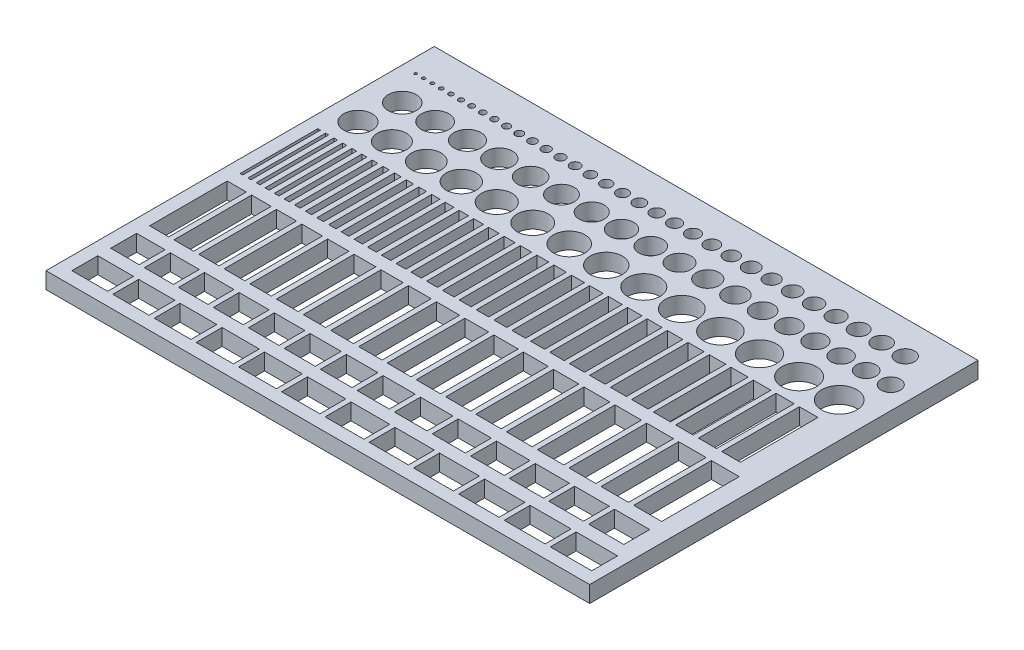
SolidWorks part; units mm, degrees
ref_plane "Front Plane" through (0, 0, 0) normal (0, 0, 1) x (1, 0, 0)
ref_plane "Top Plane" through (0, 0, 0) normal (0, 1, 0) x (1, 0, 0)
ref_plane "Right Plane" through (0, 0, 0) normal (1, 0, 0) x (0, 0, -1)
sketch "Sketch1" plane through (0, 0, 0) normal (0, 1, 0) x (1, 0, 0)
  line L1 (-105, 75) -> (105, 75)
  line L2 (-105, 75) -> (-105, -75)
  line L3 (-105, -75) -> (105, -75)
  line L4 (105, 75) -> (105, -75)
  line L5 (-105, 75) -> (105, -75) construction
  line L6 (-105, -75) -> (105, 75) construction
  point P0 (0, 0)
  dimension "D1" = 150
  dimension "D2" = 210
extrude "Boss-Extrude1" add sketch "Sketch1" along normal mid plane 6.35
sketch "Sketch2" plane through (0, 3.175, 0) normal (0, 1, 0) x (1, 0, 0)
  line L1 (-105, 75) -> (-105, -75) construction
  line L3 (105, -75) -> (105, 75) construction
  line L4 (105, 75) -> (-105, 75) construction
  circle A0 centre (-99.5, 62.3) radius 0.5
  circle A1 centre (-93.1, 62.3) radius 0.7
  circle A2 centre (-96.4, 62.3) radius 0.6
  circle A3 centre (-89.6, 62.3) radius 0.8
  circle A4 centre (-85.9, 62.3) radius 0.9
  circle A5 centre (-77.9, 62.3) radius 1.1
  circle A6 centre (-73.6, 62.3) radius 1.2
  circle A7 centre (-69.1, 62.3) radius 1.3
  circle A8 centre (-64.4, 62.3) radius 1.4
  circle A9 centre (-59.5, 62.3) radius 1.5
  circle A10 centre (-54.4, 62.3) radius 1.6
  circle A11 centre (-49.1, 62.3) radius 1.7
  circle A12 centre (-43.6, 62.3) radius 1.8
  circle A13 centre (-37.9, 62.3) radius 1.9
  circle A14 centre (-32, 62.3) radius 2
  circle A15 centre (-25.9, 62.3) radius 2.1
  circle A16 centre (-19.6, 62.3) radius 2.2
  circle A17 centre (-13.1, 62.3) radius 2.3
  circle A18 centre (-82, 62.3) radius 1
  circle A19 centre (-6.4, 62.3) radius 2.4
  circle A20 centre (0.5, 62.3) radius 2.5
  circle A21 centre (7.6, 62.3) radius 2.6
  circle A22 centre (22.4, 62.3) radius 2.8
  circle A23 centre (38, 62.3) radius 2.9
  circle A24 centre (30.1, 62.3) radius 3
  circle A25 centre (46.1, 62.3) radius 3.1
  circle A26 centre (54.4, 62.3) radius 3.2
  circle A27 centre (14.9, 62.3) radius 2.7
  circle A28 centre (62.9, 62.3) radius 3.3
  circle A29 centre (71.6, 62.3) radius 3.4
  circle A30 centre (80.5, 62.3) radius 3.5
  circle A31 centre (89.6, 62.3) radius 3.6
  dimension "D2" = 1
  dimension "D3" = 1.2
  dimension "D4" = 1.4
  dimension "D5" = 1.6
  dimension "D6" = 1.8
  dimension "D7" = 2
  dimension "D8" = 2.2
  dimension "D9" = 2.4
  dimension "D10" = 2.6
  dimension "D11" = 2.8
  dimension "D12" = 3
  dimension "D13" = 3.2
  dimension "D14" = 3.4
  dimension "D15" = 3.6
  dimension "D16" = 3.8
  dimension "D17" = 4
  dimension "D18" = 4.2
  dimension "D19" = 4.4
  dimension "D20" = 4.6
  dimension "D21" = 4.8
  dimension "D22" = 5
  dimension "D23" = 5.2
  dimension "D24" = 5.4
  dimension "D25" = 5.6
  dimension "D26" = 5.8
  dimension "D27" = 6
  dimension "D28" = 6.2
  dimension "D29" = 6.4
  dimension "D30" = 6.6
  dimension "D31" = 6.8
  dimension "D32" = 7
  dimension "D65" = 194.6
  dimension "D33" = 7.2
  dimension "D1" = 12.7
  dimension "D34" = 5.5
  dimension "D35" = 8.6
  dimension "D36" = 11.9
  dimension "D37" = 15.4
  dimension "D38" = 19.1
  dimension "D39" = 23
  dimension "D40" = 27.1
  dimension "D41" = 31.4
  dimension "D42" = 35.9
  dimension "D43" = 40.6
  dimension "D44" = 45.5
  dimension "D45" = 50.6
  dimension "D46" = 55.9
  dimension "D47" = 61.4
  dimension "D48" = 67.1
  dimension "D49" = 73
  dimension "D50" = 79.1
  dimension "D51" = 85.4
  dimension "D52" = 91.9
  dimension "D53" = 98.6
  dimension "D54" = 105.5
  dimension "D55" = 112.6
  dimension "D56" = 119.9
  dimension "D57" = 127.4
  dimension "D58" = 135.1
  dimension "D59" = 143
  dimension "D60" = 151.1
  dimension "D61" = 159.4
  dimension "D62" = 167.9
  dimension "D63" = 176.6
  dimension "D64" = 185.5
sketch "Sketch3" plane through (0, 3.175, 0) normal (0, 1, 0) x (1, 0, 0)
  line L0 (105, 75) -> (-105, 75) construction
  line L1 (105, -75) -> (105, 75) construction
  circle A0 centre (96.3, 50) radius 3.7
  circle A1 centre (86.8, 50) radius 3.8
  circle A2 centre (77.1, 50) radius 3.9
  circle A3 centre (67.2, 50) radius 4
  circle A4 centre (57.1, 50) radius 4.1
  circle A5 centre (46.8, 50) radius 4.2
  circle A6 centre (36.3, 50) radius 4.3
  circle A7 centre (25.6, 50) radius 4.4
  circle A8 centre (14.7, 50) radius 4.5
  circle A9 centre (3.6, 50) radius 4.6
  circle A10 centre (-7.7, 50) radius 4.7
  circle A11 centre (-19.2, 50) radius 4.8
  circle A12 centre (-30.9, 50) radius 4.9
  circle A13 centre (-42.8, 50) radius 5
  circle A14 centre (-54.9, 50) radius 5.1
  circle A15 centre (-67.2, 50) radius 5.2
  circle A16 centre (-79.7, 50) radius 5.3
  circle A17 centre (-92.4, 50) radius 5.4
  dimension "D9" = 8.8
  dimension "D8" = 8.6
  dimension "D7" = 8.4
  dimension "D6" = 8.2
  dimension "D5" = 8
  dimension "D4" = 7.8
  dimension "D3" = 7.6
  dimension "D2" = 7.4
  dimension "D29" = 101.4
  dimension "D28" = 90.3
  dimension "D27" = 79.4
  dimension "D26" = 68.7
  dimension "D25" = 58.2
  dimension "D24" = 47.9
  dimension "D23" = 37.8
  dimension "D22" = 27.9
  dimension "D21" = 18.2
  dimension "D20" = 8.7
  dimension "D19" = 10.8
  dimension "D18" = 10.6
  dimension "D17" = 10.4
  dimension "D16" = 10.2
  dimension "D15" = 10
  dimension "D14" = 9.8
  dimension "D13" = 9.6
  dimension "D12" = 9.4
  dimension "D11" = 9.2
  dimension "D10" = 9
  dimension "D1" = 25
  dimension "D30" = 112.7
  dimension "D31" = 124.2
  dimension "D32" = 135.9
  dimension "D33" = 147.8
  dimension "D34" = 159.9
  dimension "D35" = 172.2
  dimension "D36" = 184.7
  dimension "D37" = 197.4
sketch "Sketch4" plane through (0, 3.175, 0) normal (0, 1, 0) x (1, 0, 0)
  line L0 (105, 75) -> (-105, 75) construction
  line L1 (-105, 75) -> (-105, -75) construction
  circle A0 centre (-94.5, 35) radius 5.5
  circle A1 centre (-81.4, 35) radius 5.6
  circle A2 centre (-68.1, 35) radius 5.7
  circle A3 centre (-54.6, 35) radius 5.8
  circle A4 centre (-40.9, 35) radius 5.9
  circle A5 centre (-27, 35) radius 6
  circle A6 centre (-12.9, 35) radius 6.1
  circle A7 centre (1.4, 35) radius 6.2
  circle A8 centre (15.9, 35) radius 6.3
  circle A9 centre (30.6, 35) radius 6.4
  circle A10 centre (45.5, 35) radius 6.5
  circle A11 centre (60.6, 35) radius 6.6
  circle A12 centre (75.9, 35) radius 6.7
  circle A13 centre (91.4, 35) radius 6.8
  dimension "D21" = 78
  dimension "D2" = 11
  dimension "D4" = 11.4
  dimension "D3" = 11.2
  dimension "D7" = 12
  dimension "D6" = 11.8
  dimension "D5" = 11.6
  dimension "D10" = 12.6
  dimension "D9" = 12.4
  dimension "D8" = 12.2
  dimension "D12" = 13
  dimension "D11" = 12.8
  dimension "D15" = 13.6
  dimension "D14" = 13.4
  dimension "D13" = 13.2
  dimension "D17" = 23.6
  dimension "D16" = 10.5
  dimension "D20" = 64.1
  dimension "D19" = 50.4
  dimension "D18" = 36.9
  dimension "D28" = 180.9
  dimension "D1" = 40
  dimension "D22" = 92.1
  dimension "D23" = 106.4
  dimension "D24" = 120.9
  dimension "D25" = 135.6
  dimension "D26" = 150.5
  dimension "D27" = 165.6
  dimension "D29" = 196.4
sketch "Sketch5" plane through (0, 3.175, 0) normal (0, 1, 0) x (1, 0, 0)
  line L0 (-86.8, 25) -> (-85, 25)
  line L1 (-100, 25) -> (-99, 25)
  line L2 (-100, 25) -> (-100, -5)
  line L3 (-100, -5) -> (-99, -5)
  line L4 (-99, 25) -> (-99, -5)
  line L5 (-97, 25) -> (-95.8, 25)
  line L6 (-97, 25) -> (-97, -5)
  line L7 (-97, -5) -> (-95.8, -5)
  line L8 (-95.8, 25) -> (-95.8, -5)
  line L9 (-93.8, 25) -> (-92.4, 25)
  line L10 (-93.8, 25) -> (-93.8, -5)
  line L11 (-93.8, -5) -> (-92.4, -5)
  line L12 (-92.4, 25) -> (-92.4, -5)
  line L13 (-90.4, 25) -> (-88.8, 25)
  line L14 (-90.4, 25) -> (-90.4, -5)
  line L15 (-90.4, -5) -> (-88.8, -5)
  line L16 (-88.8, 25) -> (-88.8, -5)
  line L17 (-86.8, 25) -> (-86.8, -5)
  line L18 (-86.8, -5) -> (-85, -5)
  line L19 (-85, 25) -> (-85, -5)
  line L20 (-83, 25) -> (-81, 25)
  line L21 (-83, 25) -> (-83, -5)
  line L22 (-83, -5) -> (-81, -5)
  line L23 (-81, 25) -> (-81, -5)
  line L24 (-79, 25) -> (-76.8, 25)
  line L25 (-79, 25) -> (-79, -5)
  line L26 (-79, -5) -> (-76.8, -5)
  line L27 (-76.8, 25) -> (-76.8, -5)
  line L28 (-74.8, 25) -> (-72.4, 25)
  line L29 (-74.8, 25) -> (-74.8, -5)
  line L30 (-74.8, -5) -> (-72.4, -5)
  line L31 (-72.4, 25) -> (-72.4, -5)
  line L32 (-50.8, 25) -> (-47.4, 25)
  line L33 (-70.4, 25) -> (-67.8, 25)
  line L34 (-70.4, 25) -> (-70.4, -5)
  line L35 (-70.4, -5) -> (-67.8, -5)
  line L36 (-67.8, 25) -> (-67.8, -5)
  line L37 (-65.8, 25) -> (-63, 25)
  line L38 (-65.8, 25) -> (-65.8, -5)
  line L39 (-65.8, -5) -> (-63, -5)
  line L40 (-63, 25) -> (-63, -5)
  line L41 (-61, 25) -> (-58, 25)
  line L42 (-61, 25) -> (-61, -5)
  line L43 (-61, -5) -> (-58, -5)
  line L44 (-58, 25) -> (-58, -5)
  line L45 (-56, 25) -> (-52.8, 25)
  line L46 (-56, 25) -> (-56, -5)
  line L47 (-56, -5) -> (-52.8, -5)
  line L48 (-52.8, 25) -> (-52.8, -5)
  line L49 (-50.8, 25) -> (-50.8, -5)
  line L50 (-50.8, -5) -> (-47.4, -5)
  line L51 (-47.4, 25) -> (-47.4, -5)
  line L52 (-45.4, 25) -> (-41.8, 25)
  line L53 (-45.4, 25) -> (-45.4, -5)
  line L54 (-45.4, -5) -> (-41.8, -5)
  line L55 (-41.8, 25) -> (-41.8, -5)
  line L56 (-39.8, 25) -> (-36, 25)
  line L57 (-39.8, 25) -> (-39.8, -5)
  line L58 (-39.8, -5) -> (-36, -5)
  line L59 (-36, 25) -> (-36, -5)
  line L60 (-34, 25) -> (-30, 25)
  line L61 (-34, 25) -> (-34, -5)
  line L62 (-34, -5) -> (-30, -5)
  line L63 (-30, 25) -> (-30, -5)
  line L64 (-2, 25) -> (3, 25)
  line L65 (-28, 25) -> (-23.8, 25)
  line L66 (-28, 25) -> (-28, -5)
  line L67 (-28, -5) -> (-23.8, -5)
  line L68 (-23.8, 25) -> (-23.8, -5)
  line L69 (-21.8, 25) -> (-17.4, 25)
  line L70 (-21.8, 25) -> (-21.8, -5)
  line L71 (-21.8, -5) -> (-17.4, -5)
  line L72 (-17.4, 25) -> (-17.4, -5)
  line L73 (-15.4, 25) -> (-10.8, 25)
  line L74 (-15.4, 25) -> (-15.4, -5)
  line L75 (-15.4, -5) -> (-10.8, -5)
  line L76 (-10.8, 25) -> (-10.8, -5)
  line L77 (-8.8, 25) -> (-4, 25)
  line L78 (-8.8, 25) -> (-8.8, -5)
  line L79 (-8.8, -5) -> (-4, -5)
  line L80 (-4, 25) -> (-4, -5)
  line L81 (-2, 25) -> (-2, -5)
  line L82 (-2, -5) -> (3, -5)
  line L83 (3, 25) -> (3, -5)
  line L84 (5, 25) -> (10.2, 25)
  line L85 (5, 25) -> (5, -5)
  line L86 (5, -5) -> (10.2, -5)
  line L87 (10.2, 25) -> (10.2, -5)
  line L88 (12.2, 25) -> (17.6, 25)
  line L89 (12.2, 25) -> (12.2, -5)
  line L90 (12.2, -5) -> (17.6, -5)
  line L91 (17.6, 25) -> (17.6, -5)
  line L92 (19.6, 25) -> (25.2, 25)
  line L93 (19.6, 25) -> (19.6, -5)
  line L94 (19.6, -5) -> (25.2, -5)
  line L95 (25.2, 25) -> (25.2, -5)
  line L96 (59.6, 25) -> (66.2, 25)
  line L97 (27.2, 25) -> (33, 25)
  line L98 (27.2, 25) -> (27.2, -5)
  line L99 (27.2, -5) -> (33, -5)
  line L100 (33, 25) -> (33, -5)
  line L101 (35, 25) -> (41, 25)
  line L102 (35, 25) -> (35, -5)
  line L103 (35, -5) -> (41, -5)
  line L104 (41, 25) -> (41, -5)
  line L105 (43, 25) -> (49.2, 25)
  line L106 (43, 25) -> (43, -5)
  line L107 (43, -5) -> (49.2, -5)
  line L108 (49.2, 25) -> (49.2, -5)
  line L109 (51.2, 25) -> (57.6, 25)
  line L110 (51.2, 25) -> (51.2, -5)
  line L111 (51.2, -5) -> (57.6, -5)
  line L112 (57.6, 25) -> (57.6, -5)
  line L113 (59.6, 25) -> (59.6, -5)
  line L114 (59.6, -5) -> (66.2, -5)
  line L115 (66.2, 25) -> (66.2, -5)
  line L116 (68.2, 25) -> (75, 25)
  line L117 (68.2, 25) -> (68.2, -5)
  line L118 (68.2, -5) -> (75, -5)
  line L119 (75, 25) -> (75, -5)
  line L120 (77, 25) -> (84, 25)
  line L121 (77, 25) -> (77, -5)
  line L122 (77, -5) -> (84, -5)
  line L123 (84, 25) -> (84, -5)
  line L124 (86, 25) -> (93.2, 25)
  line L125 (86, 25) -> (86, -5)
  line L126 (86, -5) -> (93.2, -5)
  line L127 (93.2, 25) -> (93.2, -5)
  line L128 (-99, -5) -> (-97, -5) construction
  line L129 (-95.8, -5) -> (-93.8, -5) construction
  line L130 (-92.4, -5) -> (-90.4, -5) construction
  line L131 (-88.8, -5) -> (-86.8, -5) construction
  line L133 (-85, -5) -> (-83, -5) construction
  line L134 (-81, -5) -> (-79, -5) construction
  line L135 (-76.8, -5) -> (-74.8, -5) construction
  line L136 (-72.4, -5) -> (-70.4, -5) construction
  line L137 (-67.8, -5) -> (-65.8, -5) construction
  line L138 (-63, -5) -> (-61, -5) construction
  line L139 (-58, -5) -> (-56, -5) construction
  line L140 (-52.8, -5) -> (-50.8, -5) construction
  line L141 (-47.4, -5) -> (-45.4, -5) construction
  line L142 (-41.8, -5) -> (-39.8, -5) construction
  line L143 (-36, -5) -> (-34, -5) construction
  line L144 (-30, -5) -> (-28, -5) construction
  line L145 (-23.8, -5) -> (-21.8, -5) construction
  line L146 (-17.4, -5) -> (-15.4, -5) construction
  line L148 (-10.8, -5) -> (-8.8, -5) construction
  line L149 (-4, -5) -> (-2, -5) construction
  line L150 (3, -5) -> (5, -5) construction
  line L151 (10.2, -5) -> (12.2, -5) construction
  line L152 (17.6, -5) -> (19.6, -5) construction
  line L154 (25.2, -5) -> (27.2, -5) construction
  line L155 (33, -5) -> (35, -5) construction
  line L156 (41, -5) -> (43, -5) construction
  line L157 (49.2, -5) -> (51.2, -5) construction
  line L159 (57.6, -5) -> (59.6, -5) construction
  line L160 (66.2, -5) -> (68.2, -5) construction
  line L161 (75, -5) -> (77, -5) construction
  line L162 (84, -5) -> (86, -5) construction
  line L164 (-105, 75) -> (-105, -75) construction
  line L165 (105, -75) -> (105, 75) construction
  line L166 (105, 75) -> (-105, 75) construction
  dimension "D1" = 30
  dimension "D2" = 2
  dimension "D4" = 5
  dimension "D5" = 1
  dimension "D6" = 1.2
  dimension "D7" = 1.4
  dimension "D8" = 1.6
  dimension "D9" = 1.8
  dimension "D10" = 2
  dimension "D11" = 2.2
  dimension "D12" = 2.4
  dimension "D13" = 2.6
  dimension "D14" = 2.8
  dimension "D15" = 3
  dimension "D16" = 3.2
  dimension "D17" = 3.4
  dimension "D18" = 3.6
  dimension "D19" = 3.8
  dimension "D20" = 4
  dimension "D21" = 4.2
  dimension "D22" = 4.4
  dimension "D23" = 4.6
  dimension "D24" = 4.8
  dimension "D25" = 5
  dimension "D26" = 5.2
  dimension "D27" = 5.4
  dimension "D28" = 5.6
  dimension "D29" = 5.8
  dimension "D30" = 6
  dimension "D31" = 6.2
  dimension "D32" = 6.4
  dimension "D33" = 6.6
  dimension "D34" = 6.8
  dimension "D35" = 7
  dimension "D36" = 7.2
  dimension "D37" = 50
sketch "Sketch6" plane through (0, 3.175, 0) normal (0, 1, 0) x (1, 0, 0)
  line L0 (-92.6, -40) -> (-90.6, -40) construction
  line L1 (-100, -10) -> (-92.6, -10)
  line L2 (-100, -10) -> (-100, -40)
  line L3 (-100, -40) -> (-92.6, -40)
  line L4 (-92.6, -10) -> (-92.6, -40)
  line L5 (-90.6, -10) -> (-83, -10)
  line L6 (-90.6, -10) -> (-90.6, -40)
  line L7 (-90.6, -40) -> (-83, -40)
  line L8 (-83, -10) -> (-83, -40)
  line L9 (-81, -10) -> (-73.2, -10)
  line L10 (-81, -10) -> (-81, -40)
  line L11 (-81, -40) -> (-73.2, -40)
  line L12 (-73.2, -10) -> (-73.2, -40)
  line L13 (-71.2, -10) -> (-63.2, -10)
  line L14 (-71.2, -10) -> (-71.2, -40)
  line L15 (-71.2, -40) -> (-63.2, -40)
  line L16 (-63.2, -10) -> (-63.2, -40)
  line L17 (-61.2, -10) -> (-53, -10)
  line L18 (-61.2, -10) -> (-61.2, -40)
  line L19 (-61.2, -40) -> (-53, -40)
  line L20 (-53, -10) -> (-53, -40)
  line L21 (-51, -10) -> (-42.6, -10)
  line L22 (-51, -10) -> (-51, -40)
  line L23 (-51, -40) -> (-42.6, -40)
  line L24 (-42.6, -10) -> (-42.6, -40)
  line L25 (-40.6, -10) -> (-32, -10)
  line L26 (-40.6, -10) -> (-40.6, -40)
  line L27 (-40.6, -40) -> (-32, -40)
  line L28 (-32, -10) -> (-32, -40)
  line L29 (-30, -10) -> (-21.2, -10)
  line L30 (-30, -10) -> (-30, -40)
  line L31 (-30, -40) -> (-21.2, -40)
  line L32 (-21.2, -10) -> (-21.2, -40)
  line L33 (-83, -40) -> (-81, -40) construction
  line L34 (-73.2, -40) -> (-71.2, -40) construction
  line L35 (-63.2, -40) -> (-61.2, -40) construction
  line L36 (-53, -40) -> (-51, -40) construction
  line L37 (-42.6, -40) -> (-40.6, -40) construction
  line L38 (-32, -40) -> (-30, -40) construction
  line L39 (-10.2, -40) -> (-8.2, -40) construction
  line L40 (-19.2, -10) -> (-10.2, -10)
  line L41 (-19.2, -10) -> (-19.2, -40)
  line L42 (-19.2, -40) -> (-10.2, -40)
  line L43 (-10.2, -10) -> (-10.2, -40)
  line L44 (-8.2, -10) -> (1, -10)
  line L45 (-8.2, -10) -> (-8.2, -40)
  line L46 (-8.2, -40) -> (1, -40)
  line L47 (1, -10) -> (1, -40)
  line L48 (3, -10) -> (12.4, -10)
  line L49 (3, -10) -> (3, -40)
  line L50 (3, -40) -> (12.4, -40)
  line L51 (12.4, -10) -> (12.4, -40)
  line L52 (14.4, -10) -> (24, -10)
  line L53 (14.4, -10) -> (14.4, -40)
  line L54 (14.4, -40) -> (24, -40)
  line L55 (24, -10) -> (24, -40)
  line L56 (26, -10) -> (35.8, -10)
  line L57 (26, -10) -> (26, -40)
  line L58 (26, -40) -> (35.8, -40)
  line L59 (35.8, -10) -> (35.8, -40)
  line L60 (37.8, -10) -> (47.8, -10)
  line L61 (37.8, -10) -> (37.8, -40)
  line L62 (37.8, -40) -> (47.8, -40)
  line L63 (47.8, -10) -> (47.8, -40)
  line L64 (49.8, -10) -> (60, -10)
  line L65 (49.8, -10) -> (49.8, -40)
  line L66 (49.8, -40) -> (60, -40)
  line L67 (60, -10) -> (60, -40)
  line L68 (62, -10) -> (72.4, -10)
  line L69 (62, -10) -> (62, -40)
  line L70 (62, -40) -> (72.4, -40)
  line L71 (72.4, -10) -> (72.4, -40)
  line L72 (1, -40) -> (3, -40) construction
  line L73 (12.4, -40) -> (14.4, -40) construction
  line L74 (24, -40) -> (26, -40) construction
  line L75 (35.8, -40) -> (37.8, -40) construction
  line L76 (47.8, -40) -> (49.8, -40) construction
  line L77 (60, -40) -> (62, -40) construction
  line L78 (85, -40) -> (87, -40) construction
  line L79 (74.4, -10) -> (85, -10)
  line L80 (74.4, -10) -> (74.4, -40)
  line L81 (74.4, -40) -> (85, -40)
  line L82 (85, -10) -> (85, -40)
  line L83 (87, -10) -> (97.8, -10)
  line L84 (87, -10) -> (87, -40)
  line L85 (87, -40) -> (97.8, -40)
  line L86 (97.8, -10) -> (97.8, -40)
  line L87 (-100, -5) -> (-99, -5) construction
  line L156 (-21.2, -40) -> (-19.2, -40) construction
  line L157 (72.4, -40) -> (74.4, -40) construction
  line L160 (-105, 75) -> (-105, -75) construction
  dimension "D1" = 2
  dimension "D3" = 30
  dimension "D4" = 5
  dimension "D5" = 7.4
  dimension "D6" = 7.6
  dimension "D7" = 7.8
  dimension "D8" = 8
  dimension "D9" = 8.2
  dimension "D10" = 8.4
  dimension "D11" = 8.6
  dimension "D12" = 8.8
  dimension "D13" = 9
  dimension "D14" = 9.2
  dimension "D15" = 9.4
  dimension "D16" = 9.6
  dimension "D17" = 9.8
  dimension "D18" = 10
  dimension "D19" = 10.2
  dimension "D20" = 10.4
  dimension "D21" = 10.6
  dimension "D22" = 10.8
  dimension "D23" = 5
sketch "Sketch7" plane through (0, 3.175, 0) normal (0, 1, 0) x (1, 0, 0)
  line L0 (-105, 75) -> (-105, -75) construction
  line L1 (-100, -45) -> (-89, -45)
  line L2 (-100, -45) -> (-100, -55)
  line L3 (-100, -55) -> (-89, -55)
  line L4 (-89, -45) -> (-89, -55)
  line L5 (-89, -55) -> (-87, -55) construction
  line L6 (-87, -45) -> (-75.8, -45)
  line L7 (-87, -45) -> (-87, -55)
  line L8 (-87, -55) -> (-75.8, -55)
  line L9 (-75.8, -45) -> (-75.8, -55)
  line L10 (-73.8, -45) -> (-62.4, -45)
  line L11 (-73.8, -45) -> (-73.8, -55)
  line L12 (-73.8, -55) -> (-62.4, -55)
  line L13 (-62.4, -45) -> (-62.4, -55)
  line L14 (-60.4, -45) -> (-48.8, -45)
  line L15 (-60.4, -45) -> (-60.4, -55)
  line L16 (-60.4, -55) -> (-48.8, -55)
  line L17 (-48.8, -45) -> (-48.8, -55)
  line L18 (-46.8, -45) -> (-35, -45)
  line L19 (-46.8, -45) -> (-46.8, -55)
  line L20 (-46.8, -55) -> (-35, -55)
  line L21 (-35, -45) -> (-35, -55)
  line L22 (-33, -45) -> (-21, -45)
  line L23 (-33, -45) -> (-33, -55)
  line L24 (-33, -55) -> (-21, -55)
  line L25 (-21, -45) -> (-21, -55)
  line L26 (-19, -45) -> (-6.8, -45)
  line L27 (-19, -45) -> (-19, -55)
  line L28 (-19, -55) -> (-6.8, -55)
  line L29 (-6.8, -45) -> (-6.8, -55)
  line L30 (-75.8, -55) -> (-73.8, -55) construction
  line L31 (-62.4, -55) -> (-60.4, -55) construction
  line L32 (-48.8, -55) -> (-46.8, -55) construction
  line L33 (-35, -55) -> (-33, -55) construction
  line L34 (-21, -55) -> (-19, -55) construction
  line L35 (-6.8, -55) -> (-4.8, -55) construction
  line L36 (-4.8, -45) -> (7.6, -45)
  line L37 (-4.8, -45) -> (-4.8, -55)
  line L38 (-4.8, -55) -> (7.6, -55)
  line L39 (7.6, -45) -> (7.6, -55)
  line L40 (9.6, -45) -> (22.2, -45)
  line L41 (9.6, -45) -> (9.6, -55)
  line L42 (9.6, -55) -> (22.2, -55)
  line L43 (22.2, -45) -> (22.2, -55)
  line L44 (24.2, -45) -> (37, -45)
  line L45 (24.2, -45) -> (24.2, -55)
  line L46 (24.2, -55) -> (37, -55)
  line L47 (37, -45) -> (37, -55)
  line L48 (39, -45) -> (52, -45)
  line L49 (39, -45) -> (39, -55)
  line L50 (39, -55) -> (52, -55)
  line L51 (52, -45) -> (52, -55)
  line L52 (54, -45) -> (67.2, -45)
  line L53 (54, -45) -> (54, -55)
  line L54 (54, -55) -> (67.2, -55)
  line L55 (67.2, -45) -> (67.2, -55)
  line L56 (69.2, -45) -> (82.6, -45)
  line L57 (69.2, -45) -> (69.2, -55)
  line L58 (69.2, -55) -> (82.6, -55)
  line L59 (82.6, -45) -> (82.6, -55)
  line L60 (7.6, -55) -> (9.6, -55) construction
  line L61 (22.2, -55) -> (24.2, -55) construction
  line L62 (37, -55) -> (39, -55) construction
  line L63 (52, -55) -> (54, -55) construction
  line L64 (67.2, -55) -> (69.2, -55) construction
  line L65 (-100, -40) -> (-92.6, -40) construction
  line L66 (84.6, -45) -> (98.2, -45)
  line L67 (84.6, -45) -> (84.6, -55)
  line L68 (84.6, -55) -> (98.2, -55)
  line L69 (98.2, -45) -> (98.2, -55)
  line L78 (82.6, -55) -> (84.6, -55) construction
  dimension "D1" = 10
  dimension "D2" = 5
  dimension "D3" = 2
  dimension "D4" = 5
  dimension "D5" = 11
  dimension "D6" = 11.2
  dimension "D7" = 11.4
  dimension "D8" = 11.6
  dimension "D9" = 11.8
  dimension "D10" = 12
  dimension "D11" = 12.2
  dimension "D12" = 12.4
  dimension "D13" = 12.6
  dimension "D14" = 12.8
  dimension "D15" = 13
  dimension "D16" = 13.2
  dimension "D17" = 13.4
  dimension "D18" = 13.6
sketch "Sketch8" plane through (0, 3.175, 0) normal (0, 1, 0) x (1, 0, 0)
  line L0 (-86.2, -70) -> (-84.2, -70) construction
  line L1 (-100, -60) -> (-86.2, -60)
  line L2 (-100, -60) -> (-100, -70)
  line L3 (-100, -70) -> (-86.2, -70)
  line L4 (-86.2, -60) -> (-86.2, -70)
  line L5 (-84.2, -60) -> (-70.2, -60)
  line L6 (-84.2, -60) -> (-84.2, -70)
  line L7 (-84.2, -70) -> (-70.2, -70)
  line L8 (-70.2, -60) -> (-70.2, -70)
  line L9 (-68.2, -60) -> (-54, -60)
  line L10 (-68.2, -60) -> (-68.2, -70)
  line L11 (-68.2, -70) -> (-54, -70)
  line L12 (-54, -60) -> (-54, -70)
  line L13 (-52, -60) -> (-37.6, -60)
  line L14 (-52, -60) -> (-52, -70)
  line L15 (-52, -70) -> (-37.6, -70)
  line L16 (-37.6, -60) -> (-37.6, -70)
  line L17 (-35.6, -60) -> (-21, -60)
  line L18 (-35.6, -60) -> (-35.6, -70)
  line L19 (-35.6, -70) -> (-21, -70)
  line L20 (-21, -60) -> (-21, -70)
  line L21 (-19, -60) -> (-4.2, -60)
  line L22 (-19, -60) -> (-19, -70)
  line L23 (-19, -70) -> (-4.2, -70)
  line L24 (-4.2, -60) -> (-4.2, -70)
  line L25 (-2.2, -60) -> (12.8, -60)
  line L26 (-2.2, -60) -> (-2.2, -70)
  line L27 (-2.2, -70) -> (12.8, -70)
  line L28 (12.8, -60) -> (12.8, -70)
  line L29 (14.8, -60) -> (30, -60)
  line L30 (14.8, -60) -> (14.8, -70)
  line L31 (14.8, -70) -> (30, -70)
  line L32 (30, -60) -> (30, -70)
  line L33 (32, -60) -> (47.4, -60)
  line L34 (32, -60) -> (32, -70)
  line L35 (32, -70) -> (47.4, -70)
  line L36 (47.4, -60) -> (47.4, -70)
  line L37 (49.4, -60) -> (65, -60)
  line L38 (49.4, -60) -> (49.4, -70)
  line L39 (49.4, -70) -> (65, -70)
  line L40 (65, -60) -> (65, -70)
  line L41 (67, -60) -> (82.8, -60)
  line L42 (67, -60) -> (67, -70)
  line L43 (67, -70) -> (82.8, -70)
  line L44 (82.8, -60) -> (82.8, -70)
  line L45 (84.8, -60) -> (100.8, -60)
  line L46 (84.8, -60) -> (84.8, -70)
  line L47 (84.8, -70) -> (100.8, -70)
  line L48 (100.8, -60) -> (100.8, -70)
  line L65 (-70.2, -70) -> (-68.2, -70) construction
  line L66 (-54, -70) -> (-52, -70) construction
  line L67 (-37.6, -70) -> (-35.6, -70) construction
  line L68 (-21, -70) -> (-19, -70) construction
  line L69 (-4.2, -70) -> (-2.2, -70) construction
  line L70 (12.8, -70) -> (14.8, -70) construction
  line L71 (30, -70) -> (32, -70) construction
  line L72 (47.4, -70) -> (49.4, -70) construction
  line L73 (65, -70) -> (67, -70) construction
  line L74 (82.8, -70) -> (84.8, -70) construction
  line L79 (-105, 75) -> (-105, -75) construction
  line L80 (-100, -55) -> (-89, -55) construction
  dimension "D1" = 5
  dimension "D2" = 10
  dimension "D3" = 5
  dimension "D4" = 2
  dimension "D5" = 13.8
  dimension "D6" = 14
  dimension "D7" = 14.2
  dimension "D8" = 14.4
  dimension "D9" = 14.6
  dimension "D10" = 14.8
  dimension "D11" = 15
  dimension "D12" = 15.2
  dimension "D13" = 15.4
  dimension "D14" = 15.6
  dimension "D15" = 15.8
  dimension "D16" = 16
extrude "Cut-Extrude1" cut sketch "Sketch2" against normal through all
extrude "Cut-Extrude2" cut sketch "Sketch3" against normal through all
extrude "Cut-Extrude3" cut sketch "Sketch4" against normal through all
extrude "Cut-Extrude4" cut sketch "Sketch5" against normal through all
extrude "Cut-Extrude5" cut sketch "Sketch6" against normal through all
extrude "Cut-Extrude6" cut sketch "Sketch7" against normal through all
extrude "Cut-Extrude7" cut sketch "Sketch8" against normal through all
equation "\"EdgeDist1\" = 3"
equation "\"EdgeDist2\" = 3"
equation "\"EdgeDist3\" = 3"
equation "\"InitHole\" = 1"
equation "\"HoleChg\" = 0.2"
equation "\"HoleSep\" = 2"
equation "\"InitSlot\" = 1"
equation "\"SlotChg\" = 0.2"
equation "\"D2@Sketch2\" = \"InitHole\"+\"HoleChg\"*0"
equation "\"D3@Sketch2\" = \"InitHole\"+\"HoleChg\"*1"
equation "\"D4@Sketch2\" = \"InitHole\"+\"HoleChg\"*2"
equation "\"D5@Sketch2\" = \"InitHole\"+\"HoleChg\"*3"
equation "\"D6@Sketch2\" = \"InitHole\"+\"HoleChg\"*4"
equation "\"D7@Sketch2\" = \"InitHole\"+\"HoleChg\"*5"
equation "\"D8@Sketch2\" = \"InitHole\"+\"HoleChg\"*6"
equation "\"D9@Sketch2\" = \"InitHole\"+\"HoleChg\"*7"
equation "\"D10@Sketch2\" = \"InitHole\"+\"HoleChg\"*8"
equation "\"D11@Sketch2\" = \"InitHole\"+\"HoleChg\"*9"
equation "\"D12@Sketch2\" = \"InitHole\"+\"HoleChg\"*10"
equation "\"D13@Sketch2\" = \"InitHole\"+\"HoleChg\"*11"
equation "\"D14@Sketch2\" = \"InitHole\"+\"HoleChg\"*12"
equation "\"D15@Sketch2\" = \"InitHole\"+\"HoleChg\"*13"
equation "\"D16@Sketch2\" = \"InitHole\"+\"HoleChg\"*14"
equation "\"D17@Sketch2\" = \"InitHole\"+\"HoleChg\"*15"
equation "\"D18@Sketch2\" = \"InitHole\"+\"HoleChg\"*16"
equation "\"D19@Sketch2\" = \"InitHole\"+\"HoleChg\"*17"
equation "\"D20@Sketch2\" = \"InitHole\"+\"HoleChg\"*18"
equation "\"D21@Sketch2\" = \"InitHole\"+\"HoleChg\"*19"
equation "\"D22@Sketch2\" = \"InitHole\"+\"HoleChg\"*20"
equation "\"D23@Sketch2\" = \"InitHole\"+\"HoleChg\"*21"
equation "\"D24@Sketch2\" = \"InitHole\"+\"HoleChg\"*22"
equation "\"D25@Sketch2\" = \"InitHole\"+\"HoleChg\"*23"
equation "\"D26@Sketch2\" = \"InitHole\"+\"HoleChg\"*24"
equation "\"D27@Sketch2\" = \"InitHole\"+\"HoleChg\"*25"
equation "\"D28@Sketch2\" = \"InitHole\"+\"HoleChg\"*26"
equation "\"D29@Sketch2\" = \"InitHole\"+\"HoleChg\"*27"
equation "\"D30@Sketch2\" = \"InitHole\"+\"HoleChg\"*28"
equation "\"D31@Sketch2\" = \"InitHole\"+\"HoleChg\"*29"
equation "\"D32@Sketch2\" = \"InitHole\"+\"HoleChg\"*30"
equation "\"D33@Sketch2\" = \"InitHole\"+\"HoleChg\"*31"
equation "\"D34@Sketch2\" = \"EdgeDist1\" + \"HoleSep\" + \"D2@Sketch2\"/2"
equation "\"D35@Sketch2\" = \"D34@Sketch2\" + \"D2@Sketch2\"/2 + \"D3@Sketch2\"/2 + \"HoleSep\""
equation "\"D36@Sketch2\" = \"D35@Sketch2\" + \"D3@Sketch2\"/2 + \"D4@Sketch2\"/2 + \"HoleSep\""
equation "\"D37@Sketch2\" = \"D36@Sketch2\" + \"D4@Sketch2\"/2 + \"D5@Sketch2\"/2 + \"HoleSep\""
equation "\"D38@Sketch2\" = \"D37@Sketch2\" + \"D5@Sketch2\"/2 + \"D6@Sketch2\"/2 + \"HoleSep\""
equation "\"D39@Sketch2\" = \"D38@Sketch2\" + \"D6@Sketch2\"/2 + \"D7@Sketch2\"/2 + \"HoleSep\""
equation "\"D40@Sketch2\" = \"D39@Sketch2\" + \"D7@Sketch2\"/2 + \"D8@Sketch2\"/2 + \"HoleSep\""
equation "\"D41@Sketch2\" = \"D40@Sketch2\" + \"D8@Sketch2\"/2 + \"D9@Sketch2\"/2 + \"HoleSep\""
equation "\"D42@Sketch2\" = \"D41@Sketch2\" + \"D9@Sketch2\"/2 + \"D10@Sketch2\"/2 + \"HoleSep\""
equation "\"D43@Sketch2\" = \"D42@Sketch2\" + \"D10@Sketch2\"/2 + \"D11@Sketch2\"/2 + \"HoleSep\""
equation "\"D44@Sketch2\" = \"D43@Sketch2\" + \"D11@Sketch2\"/2 + \"D12@Sketch2\"/2 + \"HoleSep\""
equation "\"D45@Sketch2\" = \"D44@Sketch2\" + \"D12@Sketch2\"/2 + \"D13@Sketch2\"/2 + \"HoleSep\""
equation "\"D46@Sketch2\" = \"D45@Sketch2\" + \"D13@Sketch2\"/2 + \"D14@Sketch2\"/2 + \"HoleSep\""
equation "\"D47@Sketch2\" = \"D46@Sketch2\" + \"D14@Sketch2\"/2 + \"D15@Sketch2\"/2 + \"HoleSep\""
equation "\"D48@Sketch2\" = \"D47@Sketch2\" + \"D15@Sketch2\"/2 + \"D16@Sketch2\"/2 + \"HoleSep\""
equation "\"D49@Sketch2\" = \"D48@Sketch2\" + \"D16@Sketch2\"/2 + \"D17@Sketch2\"/2 + \"HoleSep\""
equation "\"D50@Sketch2\" = \"D49@Sketch2\" + \"D17@Sketch2\"/2 + \"D18@Sketch2\"/2 + \"HoleSep\""
equation "\"D51@Sketch2\" = \"D50@Sketch2\" + \"D18@Sketch2\"/2 + \"D19@Sketch2\"/2 + \"HoleSep\""
equation "\"D52@Sketch2\" = \"D51@Sketch2\" + \"D19@Sketch2\"/2 + \"D20@Sketch2\"/2 + \"HoleSep\""
equation "\"D53@Sketch2\" = \"D52@Sketch2\" + \"D20@Sketch2\"/2 + \"D21@Sketch2\"/2 + \"HoleSep\""
equation "\"D54@Sketch2\" = \"D53@Sketch2\" + \"D21@Sketch2\"/2 + \"D22@Sketch2\"/2 + \"HoleSep\""
equation "\"D55@Sketch2\" = \"D54@Sketch2\" + \"D22@Sketch2\"/2 + \"D23@Sketch2\"/2 + \"HoleSep\""
equation "\"D56@Sketch2\" = \"D55@Sketch2\" + \"D23@Sketch2\"/2 + \"D24@Sketch2\"/2 + \"HoleSep\""
equation "\"D57@Sketch2\" = \"D56@Sketch2\" + \"D24@Sketch2\"/2 + \"D25@Sketch2\"/2 + \"HoleSep\""
equation "\"D58@Sketch2\" = \"D57@Sketch2\" + \"D25@Sketch2\"/2 + \"D26@Sketch2\"/2 + \"HoleSep\""
equation "\"D59@Sketch2\" = \"D58@Sketch2\" + \"D26@Sketch2\"/2 + \"D27@Sketch2\"/2 + \"HoleSep\""
equation "\"D60@Sketch2\" = \"D59@Sketch2\" + \"D27@Sketch2\"/2 + \"D28@Sketch2\"/2 + \"HoleSep\""
equation "\"D61@Sketch2\" = \"D60@Sketch2\" + \"D28@Sketch2\"/2 + \"D29@Sketch2\"/2 + \"HoleSep\""
equation "\"D62@Sketch2\" = \"D61@Sketch2\" + \"D29@Sketch2\"/2 + \"D30@Sketch2\"/2 + \"HoleSep\""
equation "\"D63@Sketch2\" = \"D62@Sketch2\" + \"D30@Sketch2\"/2 + \"D31@Sketch2\"/2 + \"HoleSep\""
equation "\"D64@Sketch2\" = \"D63@Sketch2\" + \"D31@Sketch2\"/2 + \"D32@Sketch2\"/2 + \"HoleSep\""
equation "\"D65@Sketch2\" = \"D64@Sketch2\" + \"D32@Sketch2\"/2 + \"D33@Sketch2\"/2 + \"HoleSep\""
equation "\"D2@Sketch3\" = \"InitHole\"+\"HoleChg\"*32"
equation "\"D3@Sketch3\" = \"InitHole\"+\"HoleChg\"*33"
equation "\"D4@Sketch3\" = \"InitHole\"+\"HoleChg\"*34"
equation "\"D5@Sketch3\" = \"InitHole\"+\"HoleChg\"*35"
equation "\"D6@Sketch3\" = \"InitHole\"+\"HoleChg\"*36"
equation "\"D7@Sketch3\" = \"InitHole\"+\"HoleChg\"*37"
equation "\"D8@Sketch3\" = \"InitHole\"+\"HoleChg\"*38"
equation "\"D9@Sketch3\" = \"InitHole\"+\"HoleChg\"*39"
equation "\"D10@Sketch3\" = \"InitHole\"+\"HoleChg\"*40"
equation "\"D11@Sketch3\" = \"InitHole\"+\"HoleChg\"*41"
equation "\"D12@Sketch3\" = \"InitHole\"+\"HoleChg\"*42"
equation "\"D13@Sketch3\" = \"InitHole\"+\"HoleChg\"*43"
equation "\"D14@Sketch3\" = \"InitHole\"+\"HoleChg\"*44"
equation "\"D15@Sketch3\" = \"InitHole\"+\"HoleChg\"*45"
equation "\"D16@Sketch3\" = \"InitHole\"+\"HoleChg\"*46"
equation "\"D17@Sketch3\" = \"InitHole\"+\"HoleChg\"*47"
equation "\"D18@Sketch3\" = \"InitHole\"+\"HoleChg\"*48"
equation "\"D19@Sketch3\" = \"InitHole\"+\"HoleChg\"*49"
equation "\"D20@Sketch3\" = \"EdgeDist2\" + \"HoleSep\" + \"D2@Sketch3\"/2"
equation "\"D21@Sketch3\" = \"D20@Sketch3\" + \"D2@Sketch3\"/2 + \"D3@Sketch3\"/2 + \"HoleSep\""
equation "\"D22@Sketch3\" = \"D21@Sketch3\" + \"D3@Sketch3\"/2 + \"D4@Sketch3\"/2 + \"HoleSep\""
equation "\"D23@Sketch3\" = \"D22@Sketch3\" + \"D4@Sketch3\"/2 + \"D5@Sketch3\"/2 + \"HoleSep\""
equation "\"D24@Sketch3\" = \"D23@Sketch3\" + \"D5@Sketch3\"/2 + \"D6@Sketch3\"/2 + \"HoleSep\""
equation "\"D25@Sketch3\" = \"D24@Sketch3\" + \"D6@Sketch3\"/2 + \"D7@Sketch3\"/2 + \"HoleSep\""
equation "\"D26@Sketch3\" = \"D25@Sketch3\" + \"D7@Sketch3\"/2 + \"D8@Sketch3\"/2 + \"HoleSep\""
equation "\"D27@Sketch3\" = \"D26@Sketch3\" + \"D8@Sketch3\"/2 + \"D9@Sketch3\"/2 + \"HoleSep\""
equation "\"D28@Sketch3\" = \"D27@Sketch3\" + \"D9@Sketch3\"/2 + \"D10@Sketch3\"/2 + \"HoleSep\""
equation "\"D29@Sketch3\" = \"D28@Sketch3\" + \"D10@Sketch3\"/2 + \"D11@Sketch3\"/2 + \"HoleSep\""
equation "\"D30@Sketch3\" = \"D29@Sketch3\" + \"D11@Sketch3\"/2 + \"D12@Sketch3\"/2 + \"HoleSep\""
equation "\"D31@Sketch3\" = \"D30@Sketch3\" + \"D12@Sketch3\"/2 + \"D13@Sketch3\"/2 + \"HoleSep\""
equation "\"D32@Sketch3\" = \"D31@Sketch3\" + \"D13@Sketch3\"/2 + \"D14@Sketch3\"/2 + \"HoleSep\""
equation "\"D33@Sketch3\" = \"D32@Sketch3\" + \"D14@Sketch3\"/2 + \"D15@Sketch3\"/2 + \"HoleSep\""
equation "\"D34@Sketch3\" = \"D33@Sketch3\" + \"D15@Sketch3\"/2 + \"D16@Sketch3\"/2 + \"HoleSep\""
equation "\"D35@Sketch3\" = \"D34@Sketch3\" + \"D16@Sketch3\"/2 + \"D17@Sketch3\"/2 + \"HoleSep\""
equation "\"D36@Sketch3\" = \"D35@Sketch3\" + \"D17@Sketch3\"/2 + \"D18@Sketch3\"/2 + \"HoleSep\""
equation "\"D37@Sketch3\" = \"D36@Sketch3\" + \"D18@Sketch3\"/2 + \"D19@Sketch3\"/2 + \"HoleSep\""
equation "\"D2@Sketch4\" = \"InitHole\"+\"HoleChg\"*50"
equation "\"D3@Sketch4\" = \"InitHole\"+\"HoleChg\"*51"
equation "\"D4@Sketch4\" = \"InitHole\"+\"HoleChg\"*52"
equation "\"D5@Sketch4\" = \"InitHole\"+\"HoleChg\"*53"
equation "\"D6@Sketch4\" = \"InitHole\"+\"HoleChg\"*54"
equation "\"D7@Sketch4\" = \"InitHole\"+\"HoleChg\"*55"
equation "\"D8@Sketch4\" = \"InitHole\"+\"HoleChg\"*56"
equation "\"D9@Sketch4\" = \"InitHole\"+\"HoleChg\"*57"
equation "\"D10@Sketch4\" = \"InitHole\"+\"HoleChg\"*58"
equation "\"D11@Sketch4\" = \"InitHole\"+\"HoleChg\"*59"
equation "\"D12@Sketch4\" = \"InitHole\"+\"HoleChg\"*60"
equation "\"D13@Sketch4\" = \"InitHole\"+\"HoleChg\"*61"
equation "\"D14@Sketch4\" = \"InitHole\"+\"HoleChg\"*62"
equation "\"D15@Sketch4\" = \"InitHole\"+\"HoleChg\"*63"
equation "\"D16@Sketch4\" = \"EdgeDist3\" + \"HoleSep\" + \"D2@Sketch4\"/2"
equation "\"D17@Sketch4\" = \"D16@Sketch4\" + \"D2@Sketch4\"/2 + \"D3@Sketch4\"/2 + \"HoleSep\""
equation "\"D18@Sketch4\" = \"D17@Sketch4\" + \"D3@Sketch4\"/2 + \"D4@Sketch4\"/2 + \"HoleSep\""
equation "\"D19@Sketch4\" = \"D18@Sketch4\" + \"D4@Sketch4\"/2 + \"D5@Sketch4\"/2 + \"HoleSep\""
equation "\"D20@Sketch4\" = \"D19@Sketch4\" + \"D5@Sketch4\"/2 + \"D6@Sketch4\"/2 + \"HoleSep\""
equation "\"D21@Sketch4\" = \"D20@Sketch4\" + \"D6@Sketch4\"/2 + \"D7@Sketch4\"/2 + \"HoleSep\""
equation "\"D22@Sketch4\" = \"D21@Sketch4\" + \"D7@Sketch4\"/2 + \"D8@Sketch4\"/2 + \"HoleSep\""
equation "\"D23@Sketch4\" = \"D22@Sketch4\" + \"D8@Sketch4\"/2 + \"D9@Sketch4\"/2 + \"HoleSep\""
equation "\"D24@Sketch4\" = \"D23@Sketch4\" + \"D9@Sketch4\"/2 + \"D10@Sketch4\"/2 + \"HoleSep\""
equation "\"D25@Sketch4\" = \"D24@Sketch4\" + \"D10@Sketch4\"/2 + \"D11@Sketch4\"/2 + \"HoleSep\""
equation "\"D26@Sketch4\" = \"D25@Sketch4\" + \"D11@Sketch4\"/2 + \"D12@Sketch4\"/2 + \"HoleSep\""
equation "\"D27@Sketch4\" = \"D26@Sketch4\" + \"D12@Sketch4\"/2 + \"D13@Sketch4\"/2 + \"HoleSep\""
equation "\"D28@Sketch4\" = \"D27@Sketch4\" + \"D13@Sketch4\"/2 + \"D14@Sketch4\"/2 + \"HoleSep\""
equation "\"D29@Sketch4\" = \"D28@Sketch4\" + \"D14@Sketch4\"/2 + \"D15@Sketch4\"/2 + \"HoleSep\""
equation "\"D5@Sketch5\" = \"InitSlot\" + \"SlotChg\" * 0"
equation "\"D6@Sketch5\" = \"InitSlot\" + \"SlotChg\" * 1"
equation "\"D7@Sketch5\" = \"InitSlot\" + \"SlotChg\" * 2"
equation "\"D8@Sketch5\" = \"InitSlot\" + \"SlotChg\" * 3"
equation "\"D9@Sketch5\" = \"InitSlot\" + \"SlotChg\" * 4"
equation "\"D10@Sketch5\" = \"InitSlot\" + \"SlotChg\" * 5"
equation "\"D11@Sketch5\" = \"InitSlot\" + \"SlotChg\" * 6"
equation "\"D12@Sketch5\" = \"InitSlot\" + \"SlotChg\" * 7"
equation "\"D13@Sketch5\" = \"InitSlot\" + \"SlotChg\" * 8"
equation "\"D14@Sketch5\" = \"InitSlot\" + \"SlotChg\" * 9"
equation "\"D15@Sketch5\" = \"InitSlot\" + \"SlotChg\" * 10"
equation "\"D16@Sketch5\" = \"InitSlot\" + \"SlotChg\" * 11"
equation "\"D17@Sketch5\" = \"InitSlot\" + \"SlotChg\" * 12"
equation "\"D18@Sketch5\" = \"InitSlot\" + \"SlotChg\" * 13"
equation "\"D19@Sketch5\" = \"InitSlot\" + \"SlotChg\" * 14"
equation "\"D20@Sketch5\" = \"InitSlot\" + \"SlotChg\" * 15"
equation "\"D21@Sketch5\" = \"InitSlot\" + \"SlotChg\" * 16"
equation "\"D22@Sketch5\" = \"InitSlot\" + \"SlotChg\" * 17"
equation "\"D23@Sketch5\" = \"InitSlot\" + \"SlotChg\" * 18"
equation "\"D24@Sketch5\" = \"InitSlot\" + \"SlotChg\" * 19"
equation "\"D25@Sketch5\" = \"InitSlot\" + \"SlotChg\" * 20"
equation "\"D26@Sketch5\" = \"InitSlot\" + \"SlotChg\" * 21"
equation "\"D27@Sketch5\" = \"InitSlot\" + \"SlotChg\" * 22"
equation "\"D28@Sketch5\" = \"InitSlot\" + \"SlotChg\" * 23"
equation "\"D29@Sketch5\" = \"InitSlot\" + \"SlotChg\" * 24"
equation "\"D30@Sketch5\" = \"InitSlot\" + \"SlotChg\" * 25"
equation "\"D31@Sketch5\" = \"InitSlot\" + \"SlotChg\" * 26"
equation "\"D32@Sketch5\" = \"InitSlot\" + \"SlotChg\" * 27"
equation "\"D33@Sketch5\" = \"InitSlot\" + \"SlotChg\" * 28"
equation "\"D34@Sketch5\" = \"InitSlot\" + \"SlotChg\" * 29"
equation "\"D35@Sketch5\" = \"InitSlot\" + \"SlotChg\" * 30"
equation "\"D36@Sketch5\" = \"InitSlot\" + \"SlotChg\" * 31"
equation "\"D5@Sketch6\" = \"InitSlot\" + \"SlotChg\" * 32"
equation "\"D6@Sketch6\" = \"InitSlot\" + \"SlotChg\" * 33"
equation "\"D7@Sketch6\" = \"InitSlot\" + \"SlotChg\" * 34"
equation "\"D8@Sketch6\" = \"InitSlot\" + \"SlotChg\" * 35"
equation "\"D9@Sketch6\" = \"InitSlot\" + \"SlotChg\" * 36"
equation "\"D10@Sketch6\" = \"InitSlot\" + \"SlotChg\" * 37"
equation "\"D11@Sketch6\" = \"InitSlot\" + \"SlotChg\" * 38"
equation "\"D12@Sketch6\" = \"InitSlot\" + \"SlotChg\" * 39"
equation "\"D13@Sketch6\" = \"InitSlot\" + \"SlotChg\" * 40"
equation "\"D14@Sketch6\" = \"InitSlot\" + \"SlotChg\" * 41"
equation "\"D15@Sketch6\" = \"InitSlot\" + \"SlotChg\" * 42"
equation "\"D16@Sketch6\" = \"InitSlot\" + \"SlotChg\" * 43"
equation "\"D17@Sketch6\" = \"InitSlot\" + \"SlotChg\" * 44"
equation "\"D18@Sketch6\" = \"InitSlot\" + \"SlotChg\" * 45"
equation "\"D19@Sketch6\" = \"InitSlot\" + \"SlotChg\" * 46"
equation "\"D20@Sketch6\" = \"InitSlot\" + \"SlotChg\" * 47"
equation "\"D21@Sketch6\" = \"InitSlot\" + \"SlotChg\" * 48"
equation "\"D22@Sketch6\" = \"InitSlot\" + \"SlotChg\" * 49"
equation "\"D5@Sketch7\" = \"InitSlot\" + \"SlotChg\" * 50"
equation "\"D6@Sketch7\" = \"InitSlot\" + \"SlotChg\" * 51"
equation "\"D7@Sketch7\" = \"InitSlot\" + \"SlotChg\" * 52"
equation "\"D8@Sketch7\" = \"InitSlot\" + \"SlotChg\" * 53"
equation "\"D9@Sketch7\" = \"InitSlot\" + \"SlotChg\" * 54"
equation "\"D10@Sketch7\" = \"InitSlot\" + \"SlotChg\" * 55"
equation "\"D11@Sketch7\" = \"InitSlot\" + \"SlotChg\" * 56"
equation "\"D12@Sketch7\" = \"InitSlot\" + \"SlotChg\" * 57"
equation "\"D13@Sketch7\" = \"InitSlot\" + \"SlotChg\" * 58"
equation "\"D14@Sketch7\" = \"InitSlot\" + \"SlotChg\" * 59"
equation "\"D15@Sketch7\" = \"InitSlot\" + \"SlotChg\" * 60"
equation "\"D16@Sketch7\" = \"InitSlot\" + \"SlotChg\" * 61"
equation "\"D17@Sketch7\" = \"InitSlot\" + \"SlotChg\" * 62"
equation "\"D18@Sketch7\" = \"InitSlot\" + \"SlotChg\" * 63"
equation "\"D5@Sketch8\" = \"InitSlot\" + \"SlotChg\" * 64"
equation "\"D6@Sketch8\" = \"InitSlot\" + \"SlotChg\" * 65"
equation "\"D7@Sketch8\" = \"InitSlot\" + \"SlotChg\" * 66"
equation "\"D8@Sketch8\" = \"InitSlot\" + \"SlotChg\" * 67"
equation "\"D9@Sketch8\" = \"InitSlot\" + \"SlotChg\" * 68"
equation "\"D10@Sketch8\" = \"InitSlot\" + \"SlotChg\" * 69"
equation "\"D11@Sketch8\" = \"InitSlot\" + \"SlotChg\" * 70"
equation "\"D12@Sketch8\" = \"InitSlot\" + \"SlotChg\" * 71"
equation "\"D13@Sketch8\" = \"InitSlot\" + \"SlotChg\" * 72"
equation "\"D14@Sketch8\" = \"InitSlot\" + \"SlotChg\" * 73"
equation "\"D15@Sketch8\" = \"InitSlot\" + \"SlotChg\" * 74"
equation "\"D16@Sketch8\" = \"InitSlot\" + \"SlotChg\" * 75"
